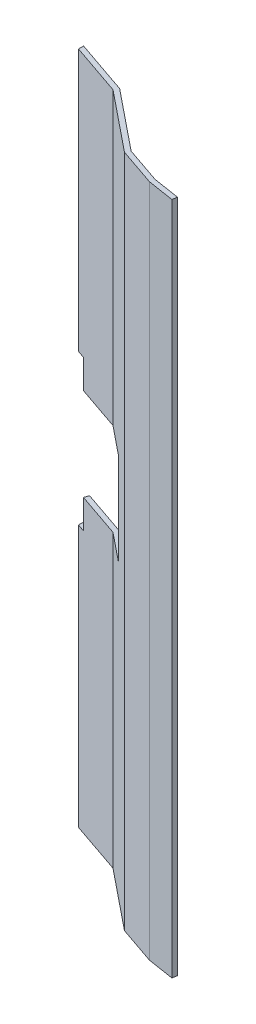
SolidWorks part; units mm, degrees
material "Alum Plate"
ref_plane "Front Plane" through (0, 0, 0) normal (0, 0, 1) x (1, 0, 0)
ref_plane "Top Plane" through (0, 0, 0) normal (0, 1, 0) x (1, 0, 0)
ref_plane "Right Plane" through (0, 0, 0) normal (1, 0, 0) x (0, 0, -1)
sketch "Sketch1" plane through (0, 0, 0) normal (0, 1, 0) x (1, 0, 0)
  point P0 (0, 0)
  line B0 (-37.0626, 23.5832) -> (-37.0626, 21.9048)
  line B1 (-18.9754, 17.3756) -> (-37.0626, 23.5832)
  line B2 (21.3237, -5.6863) -> (21.5743, -4.0939)
  line B3 (12.7923, -2.712) -> (21.5743, -4.0939)
  line B4 (-18.9754, 17.3756) -> (0.7801, 1.4107)
  line B5 (0.7801, 1.4107) -> (12.7923, -2.712)
  line B6 (21.3237, -5.6863) -> (12.5417, -4.3044)
  line B7 (12.5417, -4.3044) -> (0, 0)
  line B8 (0, 0) -> (-19.7555, 15.9649)
  line B9 (-19.7555, 15.9649) -> (-37.0626, 21.9048)
  line B10 (-37.0626, 21.9048) -> (-37.0626, 23.5832)
sketch_block_instance "Wedge sketch block-1"
sketch_block "Wedge sketch block" parameters "D1"=160, "D2"=25.4, "D3"=170, "D4"=1.5875, "D5"=1.5875, "D6"=1.5875, "D7"=160, "D8"=8.89, "D9"=8.89, "D10"=12.7
sketch "Sketch3" plane through (0, 0, 0) normal (0, 1, 0) x (1, 0, 0)
  line L0 (-37.0626, 21.9048) -> (-19.7555, 15.9649)
  line L1 (-19.7555, 15.9649) -> (0, 0)
  line L2 (0, 0) -> (12.5417, -4.3044)
  line L3 (12.5417, -4.3044) -> (21.3237, -5.6863)
  line L4 (21.3237, -5.6863) -> (21.5743, -4.0939)
  line L5 (21.5743, -4.0939) -> (12.7923, -2.712)
  line L6 (12.7923, -2.712) -> (0.7801, 1.4107)
  line L7 (0.7801, 1.4107) -> (-18.9754, 17.3756)
  line L8 (-18.9754, 17.3756) -> (-37.0626, 23.5832)
  line L9 (-37.0626, 23.5832) -> (-37.0626, 21.9048)
  dimension "D1" = 160
  dimension "D2" = 25.4
  dimension "D3" = 1.5875
  dimension "D4" = 1.5875
  dimension "D5" = 19.1227
extrude "Boss-Extrude2" add sketch "Sketch3" along normal blind 222.25
sketch "Sketch4" plane through (3.3354, 0, -9.7184) normal (0.3246, 0, -0.9458) x (-0.9458, 0, -0.3246)
  line L0 (42.711, 222.25) -> (42.711, 0) construction
  line L1 (42.711, 126.365) -> (12.231, 126.365)
  line L2 (42.711, 126.365) -> (42.711, 95.885)
  line L3 (42.711, 95.885) -> (12.231, 95.885)
  line L4 (12.231, 126.365) -> (12.231, 95.885)
  line L6 (-0.2799, 222.25) -> (23.5883, 222.25) construction
  line L7 (23.5883, 0) -> (42.711, 0) construction
  line L9 (42.711, 126.365) -> (39.536, 126.365)
  line L10 (42.711, 126.365) -> (42.711, 135.89)
  line L11 (42.711, 135.89) -> (39.536, 135.89)
  line L12 (39.536, 126.365) -> (39.536, 135.89)
  line L13 (42.711, 95.885) -> (39.536, 95.885)
  line L14 (42.711, 95.885) -> (42.711, 86.36)
  line L15 (42.711, 86.36) -> (39.536, 86.36)
  line L16 (39.536, 95.885) -> (39.536, 86.36)
  line M6 (42.711, 0) -> (42.711, 222.25)
  line M8 (23.5883, 222.25) -> (23.5883, 0)
  dimension "D1" = 95.885
  dimension "D2" = 95.885
  dimension "D3" = 30.48
  dimension "D4" = 3.175
  dimension "D5" = 3.175
  dimension "D6" = 9.525
  dimension "D7" = 9.525
extrude "Cut-Extrude2" cut sketch "Sketch4" against normal through all both and the other way through all contours L12 L1 L11 M6 | L3 L1 M6 M8 | L3 L16 L15 M6 | L1 L4 L3 M8
